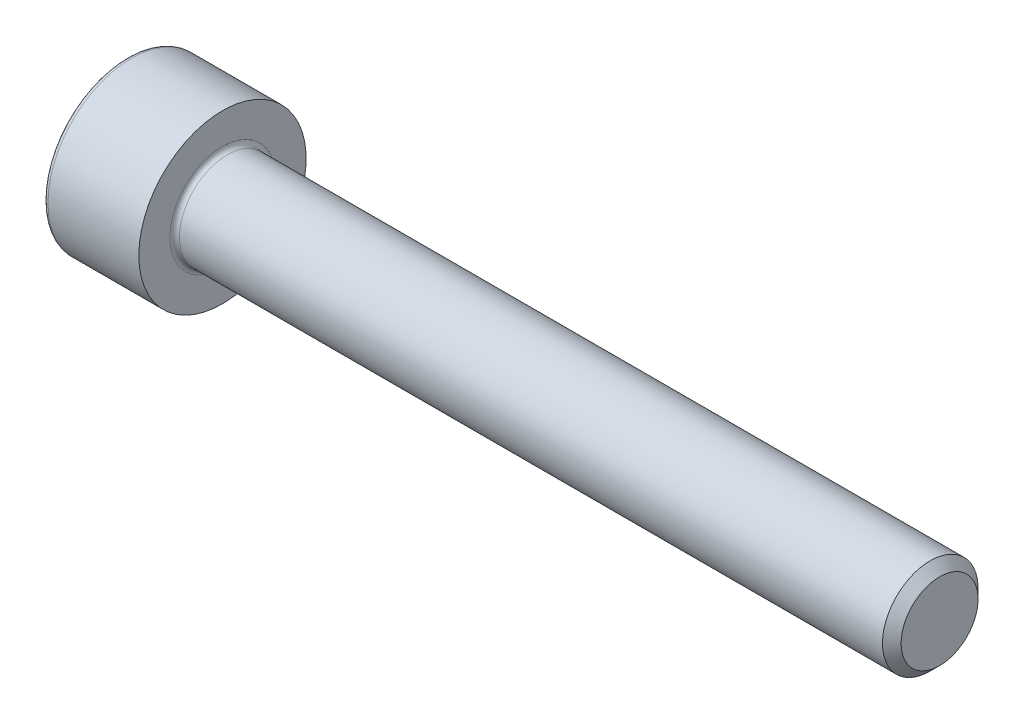
SolidWorks part; units mm, degrees
revolve "Base-Revolve" add sketch "BodySke"
sketch "BodySke" plane through (0, 0, 0) normal (0, 0, 1) x (1, 0, 0)
  line L0 (0, 0) -> (0, 3.5)
  line L1 (0, 3.5) -> (4, 3.5)
  line L2 (4, 3.5) -> (4, 2)
  line L3 (4, 2) -> (33.61, 2)
  line L4 (34, 1.61) -> (34, 0)
  line L5 (34, 0) -> (0, 0)
  line L6 (-31.75, 0) -> (127, 0) construction
  line L8 (34, 1.61) -> (33.61, 2)
  line L10 (34, -1.61) -> (33.61, -2) construction
  line L11 (4.7, 9.525) -> (4.7, 3.175) construction
  line L12 (14, 9.525) -> (14, 3.175) construction
  line L13 (-26, 9.525) -> (-26, 3.175) construction
  dimension "Head_ht" = 4
  dimension "Length" = 30
  dimension "Body_ch_ang" = 45
  dimension "Diameter" = 4
  dimension "Minor_dia" = 3.22
  dimension "Advance" = 0.7
  dimension "Thread_nom" = 20
  dimension "Thread_length" = 60
  dimension "Head_dia" = 7
cosmetic thread "ThreadCosmetic" [suppressed]
fillet "Fillet1" radius 0.2 1 edges at (4, 0, 2)
fillet "Fillet2" radius 0.2 1 edges at (0, 0, 3.5)
ref_plane "Plane1" through (0, 0, 0) normal (0, 0, 1) x (1, 0, 0)
ref_plane "Plane2" through (0, 0, 0) normal (0, 1, 0) x (1, 0, 0)
ref_plane "Plane3" through (0, 0, 0) normal (1, 0, 0) x (0, 0, -1)
sketch "Sketch2" plane through (0, 0, 0) normal (0, 0, 1) x (1, 0, 0)
  line L0 (0, 1.5355) -> (2, 1.5355)
  line L1 (2, 1.5355) -> (2.8865, 0)
  line L2 (-31.75, 0) -> (127, 0) construction
  line L3 (2.8865, 0) -> (0, 0)
  line L4 (0, 0) -> (0, 1.5355)
  line L6 (0, 0) -> (47.625, 0) construction
  dimension "D1" = 1.5355
  dimension "D2" = 60
  dimension "Depth" = 2
revolve "Hex-PreBroach" cut sketch "Sketch2" angle 360 about L6
sketch "Sketch3" plane through (0, 0, 0) normal (-1, 0, 0) x (0, 0.5, 0.866)
  line L0 (0.8865, 1.5355) -> (-0.8865, 1.5355)
  line L1 (-0.8865, 1.5355) -> (-1.773, 0)
  line L2 (0.8865, 1.5355) -> (1.773, 0)
  line L3 (0.8865, -1.5355) -> (1.773, 0)
  line L4 (0.8865, -1.5355) -> (-0.8865, -1.5355)
  line L5 (-0.8865, -1.5355) -> (-1.773, 0)
  dimension "D1" = 1.5355
  dimension "D2" = 1.5355
  dimension "Hex_size" = 3.071
extrude "Hex" cut sketch "Sketch3" against normal blind 2
sketch "ThdSchSke" plane through (0, 0, 0) normal (0, 0, 1) x (1, 0, 0)
  line L0 (14, -1.61) -> (13.7269, -2)
  line L1 (14, -1.61) -> (14.2731, -2)
  line L2 (14.2731, -2) -> (14.2731, -2.5)
  line L3 (-3.175, 0) -> (5.1513, 0) construction
  line L4 (0, 3.3) -> (0, -3.3) construction
  line L5 (14.2731, -2.5) -> (13.7269, -2.5)
  line L6 (13.7269, -2.5) -> (13.7269, -2)
  dimension "Thread_minor" = 3.22
  dimension "Diameter" = 4
  dimension "Start" = 14
revolve "ThreadSchematic" [suppressed] cut sketch "ThdSchSke" angle 360 about L3
pattern_linear "ThdSchPat" [suppressed]
equation "\"D2@Sketch3\" = \"Hex_size@Sketch3\" / 2"
equation "\"D1@Sketch3\" = \"Hex_size@Sketch3\" / 2"
equation "\"D1@Sketch2\" = \"Hex_size@Sketch3\" / 2"
equation "\"Thread_minor@ThreadCosmetic\"  =  \"Minor_dia@BodySke\""
equation "\"Depth@Sketch2\" =  \"Key_eng@Hex\""
equation "\"Thread_length@ThreadCosmetic\" = ((sgn( (\"Length@BodySke\" - \"Advance@BodySke\" * 3.0) - \"Thread_nom@BodySke\" )-1)*( (\"Length@BodySke\" - \"Advance@BodySke\" * 3.0) - \"Thread_nom@BodySke\" ))/-2+ \"Thread_nom@BodySke\""
equation "\"Thread_minor@ThdSchSke\" = \"Minor_dia@BodySke\""
equation "\"Diameter@ThdSchSke\" = \"Diameter@BodySke\""
equation "\"Overcut@ThdSchSke\" = \"Diameter@BodySke\" * 1.25"
equation "\"Start@ThdSchSke\" = \"Head_ht@BodySke\" + \"Length@BodySke\" - \"Thread_length@ThreadCosmetic\"  '---Non-countersunk---"
equation "\"Num_threads@ThdSchPat\" = int( \"Thread_length@ThreadCosmetic\" / \"Advance@BodySke\" + 0.999 )  + 1"
equation "\"Advance@ThdSchPat\" = \"Thread_length@ThreadCosmetic\" /  (\"Num_threads@ThdSchPat\" - 1) 'relax it"
equation "\"Num_threads@ThdSchPat\" = \"Num_threads@ThdSchPat\" - sgn( \"Num_threads@ThdSchPat\" - 1) '---chamfered tips only---"
